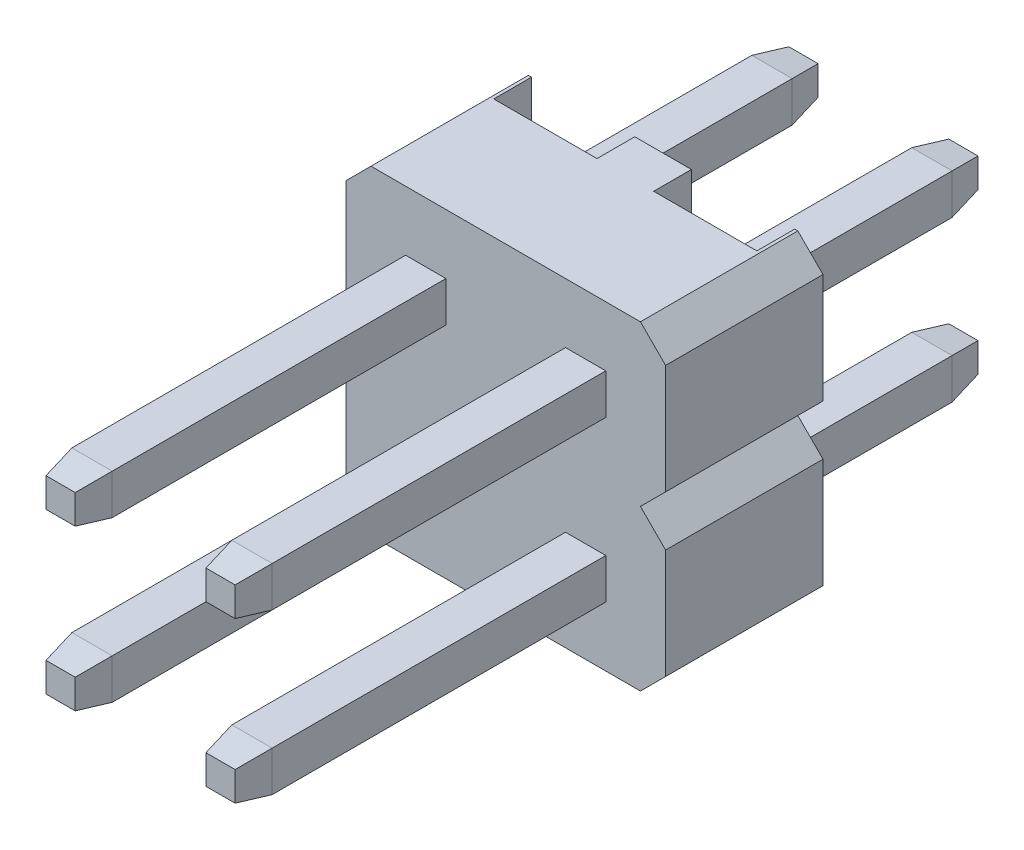
SolidWorks part; units mm, degrees
ref_plane "Płaszczyzna przednia" through (0, 0, 0) normal (0, 0, 1) x (1, 0, 0)
ref_plane "Płaszczyzna górna" through (0, 0, 0) normal (0, 1, 0) x (1, 0, 0)
ref_plane "Płaszczyzna prawa" through (0, 0, 0) normal (1, 0, 0) x (0, 0, -1)
sketch "Sketch1" plane through (0, 0, 0) normal (0, 0, 1) x (1, 0, 0)
  line L1 (1.27, 1.27) -> (-1.27, 1.27) construction
  line L2 (1.27, 1.27) -> (1.27, -1.27) construction
  line L3 (1.27, -1.27) -> (-1.27, -1.27) construction
  line L4 (-1.27, 1.27) -> (-1.27, -1.27) construction
  line L5 (1.27, 1.27) -> (-1.27, -1.27) construction
  line L6 (1.27, -1.27) -> (-1.27, 1.27) construction
  line L7 (-0.95, 0.95) -> (-1.59, 0.95)
  line L8 (-0.95, 0.95) -> (-0.95, 1.59)
  line L9 (-0.95, 1.59) -> (-1.59, 1.59)
  line L10 (-1.59, 0.95) -> (-1.59, 1.59)
  line L11 (-0.95, 0.95) -> (-1.59, 1.59) construction
  line L12 (-0.95, 1.59) -> (-1.59, 0.95) construction
  line L13 (-0.95, -0.95) -> (-1.59, -0.95)
  line L14 (-0.95, -0.95) -> (-0.95, -1.59)
  line L15 (-0.95, -1.59) -> (-1.59, -1.59)
  line L16 (-1.59, -0.95) -> (-1.59, -1.59)
  line L17 (-0.95, -0.95) -> (-1.59, -1.59) construction
  line L18 (-0.95, -1.59) -> (-1.59, -0.95) construction
  line L19 (0.95, 0.95) -> (1.59, 0.95)
  line L20 (0.95, 0.95) -> (0.95, 1.59)
  line L21 (0.95, 1.59) -> (1.59, 1.59)
  line L22 (1.59, 0.95) -> (1.59, 1.59)
  line L23 (0.95, 0.95) -> (1.59, 1.59) construction
  line L24 (0.95, 1.59) -> (1.59, 0.95) construction
  line L25 (0.95, -1.59) -> (1.59, -1.59)
  line L26 (0.95, -1.59) -> (0.95, -0.95)
  line L27 (0.95, -0.95) -> (1.59, -0.95)
  line L28 (1.59, -1.59) -> (1.59, -0.95)
  line L29 (0.95, -1.59) -> (1.59, -0.95) construction
  line L30 (0.95, -0.95) -> (1.59, -1.59) construction
  point P0 (0, 0)
extrude "Boss-Extrude1" add sketch "Sketch1" along normal blind 5.3
sketch "Sketch2" plane through (0, 0, 5.3) normal (0, 0, 1) x (1, 0, 0)
  line L4 (-1.59, -0.95) -> (-1.59, -1.59)
  line L5 (-1.59, -1.59) -> (-0.95, -1.59)
  line L6 (-0.95, -1.59) -> (-0.95, -0.95)
  line L7 (-0.95, -0.95) -> (-1.59, -0.95)
  line L8 (-1.59, -0.95) -> (-1.59, -1.59)
  line L9 (-1.59, -1.59) -> (-0.95, -1.59)
  line L10 (-0.95, -1.59) -> (-0.95, -0.95)
  line L11 (-0.95, -0.95) -> (-1.59, -0.95)
  line L12 (-1.59, 1.59) -> (-1.59, 0.95)
  line L13 (-1.59, 0.95) -> (-0.95, 0.95)
  line L14 (-0.95, 0.95) -> (-0.95, 1.59)
  line L15 (-0.95, 1.59) -> (-1.59, 1.59)
  line L16 (-1.59, 1.59) -> (-1.59, 0.95)
  line L17 (-1.59, 0.95) -> (-0.95, 0.95)
  line L18 (-0.95, 0.95) -> (-0.95, 1.59)
  line L19 (-0.95, 1.59) -> (-1.59, 1.59)
  line L20 (1.59, -1.59) -> (1.59, -0.95)
  line L21 (1.59, -0.95) -> (0.95, -0.95)
  line L22 (0.95, -0.95) -> (0.95, -1.59)
  line L23 (0.95, -1.59) -> (1.59, -1.59)
  line L24 (1.59, -1.59) -> (1.59, -0.95)
  line L25 (1.59, -0.95) -> (0.95, -0.95)
  line L26 (0.95, -0.95) -> (0.95, -1.59)
  line L27 (0.95, -1.59) -> (1.59, -1.59)
  line L28 (1.59, 0.95) -> (1.59, 1.59)
  line L29 (1.59, 1.59) -> (0.95, 1.59)
  line L30 (0.95, 1.59) -> (0.95, 0.95)
  line L31 (0.95, 0.95) -> (1.59, 0.95)
  line L32 (1.59, 0.95) -> (1.59, 1.59)
  line L33 (1.59, 1.59) -> (0.95, 1.59)
  line L34 (0.95, 1.59) -> (0.95, 0.95)
  line L35 (0.95, 0.95) -> (1.59, 0.95)
  dimension "D1" = 0
  dimension "D2" = 0
  dimension "D3" = 0
  dimension "D4" = 0
extrude "Boss-Extrude2" add sketch "Sketch2" along normal blind 0.5 draft 10
sketch "Sketch3" plane through (0, 0, 0) normal (0, 0, 1) x (1, 0, 0)
  line L1 (-2.14, 2.54) -> (2.14, 2.54)
  line L2 (-2.54, 2.14) -> (-2.54, -2.14)
  line L3 (-2.14, -2.54) -> (2.14, -2.54)
  line L4 (2.54, 2.14) -> (2.54, -2.14)
  line L5 (-2.54, 2.54) -> (2.54, -2.54) construction
  line L6 (-2.54, -2.54) -> (2.54, 2.54) construction
  line L24 (-2.54, -2.14) -> (-2.14, -2.54)
  line L25 (2.14, -2.54) -> (2.54, -2.14)
  line L26 (2.14, 2.54) -> (2.54, 2.14)
  line L27 (-2.54, 2.14) -> (-2.14, 2.54)
  point P0 (0, 0)
extrude "Boss-Extrude3" add sketch "Sketch3" against normal blind 2.5 separate body
sketch "Sketch5" plane through (0, 0, -2.5) normal (0, 0, -1) x (-1, 0, 0)
  line L0 (-0.45, -2.54) -> (-0.45, 2.54)
  line L1 (2.14, -2.54) -> (-2.14, -2.54) construction
  line L2 (-2.14, 2.54) -> (2.14, 2.54) construction
  line L3 (-2.09, -2.54) -> (-2.09, 2.54)
  line L4 (-2.54, -2.14) -> (-2.54, 2.14) construction
  line L5 (-0.95, -0.95) -> (-0.95, -1.59) construction
  line L7 (0, -2.54) -> (0, -3.101) construction
  line L8 (2.09, -2.54) -> (2.09, 2.54)
  line L9 (0.45, -2.54) -> (0.45, 2.54)
  line L10 (2.09, -2.54) -> (0.45, -2.54)
  line L11 (-0.45, -2.54) -> (-2.09, -2.54)
  line L12 (2.09, 2.54) -> (0.45, 2.54)
  line L13 (-0.45, 2.54) -> (-2.09, 2.54)
  dimension "D1" = 0.45
  dimension "D2" = 0.5
extrude "Cut-Extrude1" cut sketch "Sketch5" against normal blind 0.6
sketch "Sketch6" plane through (0, 0, 0) normal (0, 0, 1) x (1, 0, 0)
  line L0 (2.54, 0) -> (-2.54, 0) construction
  line L1 (2.54, -2.14) -> (2.54, 2.14) construction
  line L2 (-2.54, 2.14) -> (-2.54, -2.14) construction
  line L3 (-2.54, 0.05) -> (-2.54, -0.05)
  line L4 (-2.54, 0.05) -> (2.54, 0.05)
  line L5 (2.54, 0.05) -> (2.54, -0.05)
  line L6 (2.54, -0.05) -> (-2.54, -0.05)
  dimension "D1" = 0.1
sketch "Sketch7" plane through (0, 0, 0) normal (0, 0, 1) x (1, 0, 0)
  line L0 (2.54, 0.4) -> (2.14, 0)
  line L3 (2.14, 0) -> (2.54, 0)
  line L4 (2.54, 0) -> (2.54, 0.4)
  line L5 (2.54, 0) -> (2.14, 0)
  line L7 (2.14, 0) -> (2.54, -0.4)
  line L9 (2.54, -0.4) -> (2.54, 0)
  line L10 (0, -0.05) -> (0, 3.4542) construction
  line L11 (-2.54, -0.4) -> (-2.54, 0)
  line L12 (-2.14, 0) -> (-2.54, -0.4)
  line L13 (-2.54, 0) -> (-2.14, 0)
  line L14 (-2.54, 0) -> (-2.54, 0.4)
  line L15 (-2.14, 0) -> (-2.54, 0)
  line L16 (-2.54, 0.4) -> (-2.14, 0)
  line L17 (-2.54, 0) -> (2.54, 0) construction
  line L18 (-2.54, 2.14) -> (-2.54, -2.14) construction
  line L19 (2.54, -2.14) -> (2.54, 2.14) construction
extrude "Cut-Extrude3" cut sketch "Sketch7" against normal through all contours L14 L16 L15 | L11 L13 L12 | L4 L0 L3 | L9 L5 L7
sketch "Sketch8" plane through (0, 0, -1.9) normal (0, 0, -1) x (-1, 0, 0)
  line L0 (1.59, -1.59) -> (0.95, -1.59)
  line L1 (0.95, -1.59) -> (0.95, -0.95)
  line L2 (0.95, -0.95) -> (1.59, -0.95)
  line L3 (1.59, -0.95) -> (1.59, -1.59)
  line L12 (0.95, 1.59) -> (1.59, 1.59) construction
  line L13 (0.95, 0.95) -> (0.95, 1.59) construction
  line L14 (1.59, 1.59) -> (1.59, 0.95) construction
  line L15 (1.59, 0.95) -> (0.95, 0.95) construction
  line L16 (-0.95, 0.95) -> (-1.59, 0.95) construction
  line L17 (-0.95, 1.59) -> (-0.95, 0.95) construction
  line L18 (-1.59, 1.59) -> (-0.95, 1.59) construction
  line L19 (-1.59, 0.95) -> (-1.59, 1.59) construction
  line L20 (-1.59, -0.95) -> (-0.95, -0.95) construction
  line L21 (-1.59, -1.59) -> (-1.59, -0.95) construction
  line L22 (-0.95, -0.95) -> (-0.95, -1.59) construction
  line L23 (-0.95, -1.59) -> (-1.59, -1.59) construction
  line L32 (0.95, 1.59) -> (1.59, 1.59)
  line L33 (0.95, 0.95) -> (0.95, 1.59)
  line L34 (1.59, 1.59) -> (1.59, 0.95)
  line L35 (1.59, 0.95) -> (0.95, 0.95)
  line L36 (-0.95, 0.95) -> (-1.59, 0.95)
  line L37 (-0.95, 1.59) -> (-0.95, 0.95)
  line L38 (-1.59, 1.59) -> (-0.95, 1.59)
  line L39 (-1.59, 0.95) -> (-1.59, 1.59)
  line L40 (-1.59, -0.95) -> (-0.95, -0.95)
  line L41 (-1.59, -1.59) -> (-1.59, -0.95)
  line L42 (-0.95, -0.95) -> (-0.95, -1.59)
  line L43 (-0.95, -1.59) -> (-1.59, -1.59)
extrude "Boss-Extrude4" add sketch "Sketch8" along normal blind 3.6 separate body
sketch "Sketch9" plane through (0, 0, -5.5) normal (0, 0, -1) x (-1, 0, 0)
  line L4 (0.95, 1.59) -> (0.95, 0.95)
  line L5 (0.95, 0.95) -> (1.59, 0.95)
  line L6 (1.59, 0.95) -> (1.59, 1.59)
  line L7 (1.59, 1.59) -> (0.95, 1.59)
  line L8 (0.95, 1.59) -> (0.95, 0.95)
  line L9 (0.95, 0.95) -> (1.59, 0.95)
  line L10 (1.59, 0.95) -> (1.59, 1.59)
  line L11 (1.59, 1.59) -> (0.95, 1.59)
  line L12 (1.59, -1.59) -> (1.59, -0.95)
  line L13 (1.59, -0.95) -> (0.95, -0.95)
  line L14 (0.95, -0.95) -> (0.95, -1.59)
  line L15 (0.95, -1.59) -> (1.59, -1.59)
  line L16 (1.59, -1.59) -> (1.59, -0.95)
  line L17 (1.59, -0.95) -> (0.95, -0.95)
  line L18 (0.95, -0.95) -> (0.95, -1.59)
  line L19 (0.95, -1.59) -> (1.59, -1.59)
  line L20 (-1.59, -0.95) -> (-1.59, -1.59)
  line L21 (-1.59, -1.59) -> (-0.95, -1.59)
  line L22 (-0.95, -1.59) -> (-0.95, -0.95)
  line L23 (-0.95, -0.95) -> (-1.59, -0.95)
  line L24 (-1.59, -0.95) -> (-1.59, -1.59)
  line L25 (-1.59, -1.59) -> (-0.95, -1.59)
  line L26 (-0.95, -1.59) -> (-0.95, -0.95)
  line L27 (-0.95, -0.95) -> (-1.59, -0.95)
  line L28 (-0.95, 0.95) -> (-0.95, 1.59)
  line L29 (-0.95, 1.59) -> (-1.59, 1.59)
  line L30 (-1.59, 1.59) -> (-1.59, 0.95)
  line L31 (-1.59, 0.95) -> (-0.95, 0.95)
  line L32 (-0.95, 0.95) -> (-0.95, 1.59)
  line L33 (-0.95, 1.59) -> (-1.59, 1.59)
  line L34 (-1.59, 1.59) -> (-1.59, 0.95)
  line L35 (-1.59, 0.95) -> (-0.95, 0.95)
  dimension "D1" = 0
  dimension "D2" = 0
  dimension "D3" = 0
  dimension "D4" = 0
extrude "Boss-Extrude5" add sketch "Sketch9" along normal blind 0.5 draft 10
